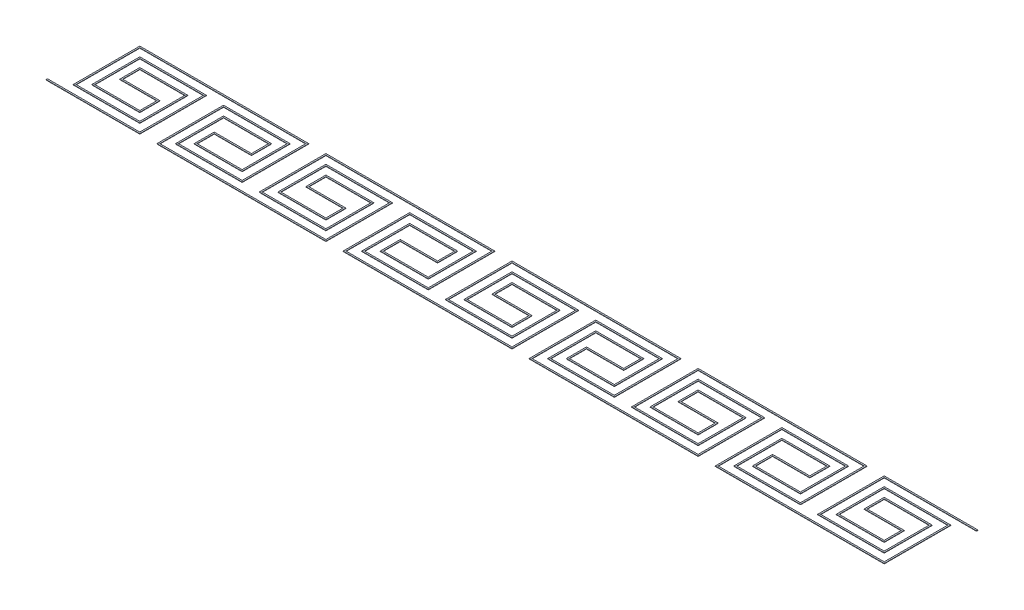
SolidWorks part; units mm, degrees
ref_plane "Front Plane" through (0, 0, 0) normal (0, 0, 1) x (1, 0, 0)
ref_plane "Top Plane" through (0, 0, 0) normal (0, 1, 0) x (1, 0, 0)
ref_plane "Right Plane" through (0, 0, 0) normal (1, 0, 0) x (0, 0, -1)
sketch "Sketch1" plane through (0, 0, 0) normal (0, 1, 0) x (1, 0, 0)
  line L0 (-0.25, 0) -> (0.25, 0)
  line L1 (-0.5, -0.5) -> (0.5, -0.5)
  line L2 (-0.5, -0.375) -> (-0.5, 0.5)
  line L3 (-0.5, 0.5) -> (0.5, 0.5)
  line L4 (0.5, -0.5) -> (0.5, 0.375)
  line L5 (-0.5, -0.5) -> (0.5, 0.5) construction
  line L6 (-0.5, 0.5) -> (0.5, -0.5) construction
  line L8 (-0.375, -0.25) -> (-0.375, 0.375)
  line L10 (0.375, -0.375) -> (0.375, 0.25)
  line L11 (-0.375, -0.375) -> (0.375, 0.375) construction
  line L12 (-0.375, 0.375) -> (0.375, -0.375) construction
  line L14 (-0.25, 0) -> (-0.25, 0.25)
  line L16 (0.25, -0.25) -> (0.25, 0)
  line L17 (-0.25, -0.25) -> (0.25, 0.25) construction
  line L18 (-0.25, 0.25) -> (0.25, -0.25) construction
  line L19 (-0.5, -0.375) -> (0.375, -0.375)
  line L20 (-0.25, 0.25) -> (0.375, 0.25)
  line L21 (-0.375, 0.375) -> (0.5, 0.375)
  line L22 (-0.5, -0.5) -> (-0.75, -0.5)
  line L23 (-0.375, -0.25) -> (0.25, -0.25)
  line L24 (-1.75, 0.5) -> (-2, 0.5)
  line L25 (-1, 0.25) -> (-1.5, -0.25) construction
  line L26 (-1, -0.25) -> (-1.5, 0.25) construction
  line L27 (-0.875, 0.375) -> (-1.625, -0.375) construction
  line L28 (-0.875, -0.375) -> (-1.625, 0.375) construction
  line L29 (-0.75, 0.5) -> (-1.75, -0.5) construction
  line L30 (-0.75, -0.5) -> (-1.75, 0.5) construction
  line L31 (-0.875, -0.25) -> (-1.5, -0.25)
  line L32 (-0.875, 0.375) -> (-1.75, 0.375)
  line L33 (-1, 0.25) -> (-1.625, 0.25)
  line L34 (-0.75, -0.375) -> (-1.625, -0.375)
  line L35 (-1.5, -0.25) -> (-1.5, 0)
  line L36 (-1, 0) -> (-1, 0.25)
  line L37 (-1.625, -0.375) -> (-1.625, 0.25)
  line L38 (-0.875, -0.25) -> (-0.875, 0.375)
  line L39 (-1.75, -0.5) -> (-1.75, 0.375)
  line L40 (-0.75, 0.5) -> (-1.75, 0.5)
  line L41 (-0.75, -0.375) -> (-0.75, 0.5)
  line L42 (-0.75, -0.5) -> (-1.75, -0.5)
  line L43 (-1, 0) -> (-1.5, 0)
  line L44 (-4.25, 0.5) -> (-4.5, 0.5)
  line L45 (-3, -0.5) -> (-2, 0.5) construction
  line L46 (-3, 0.5) -> (-2, -0.5) construction
  line L47 (-2.875, -0.375) -> (-2.125, 0.375) construction
  line L48 (-2.875, 0.375) -> (-2.125, -0.375) construction
  line L49 (-2.75, -0.25) -> (-2.25, 0.25) construction
  line L50 (-2.75, 0.25) -> (-2.25, -0.25) construction
  line L51 (-3.5, 0.25) -> (-4, -0.25) construction
  line L52 (-3.5, -0.25) -> (-4, 0.25) construction
  line L53 (-3.375, 0.375) -> (-4.125, -0.375) construction
  line L54 (-3.375, -0.375) -> (-4.125, 0.375) construction
  line L55 (-3.25, 0.5) -> (-4.25, -0.5) construction
  line L56 (-3.25, -0.5) -> (-4.25, 0.5) construction
  line L57 (-2.75, 0) -> (-2.25, 0)
  line L58 (-3, -0.5) -> (-2, -0.5)
  line L59 (-3, -0.375) -> (-3, 0.5)
  line L60 (-3, 0.5) -> (-2, 0.5)
  line L61 (-2, -0.5) -> (-2, 0.375)
  line L62 (-2.875, -0.25) -> (-2.875, 0.375)
  line L63 (-2.125, -0.375) -> (-2.125, 0.25)
  line L64 (-2.75, 0) -> (-2.75, 0.25)
  line L65 (-2.25, -0.25) -> (-2.25, 0)
  line L66 (-3, -0.375) -> (-2.125, -0.375)
  line L67 (-2.75, 0.25) -> (-2.125, 0.25)
  line L68 (-2.875, 0.375) -> (-2, 0.375)
  line L69 (-2.875, -0.25) -> (-2.25, -0.25)
  line L70 (-3.375, -0.25) -> (-4, -0.25)
  line L71 (-3.25, -0.5) -> (-3, -0.5)
  line L72 (-3.375, 0.375) -> (-4.25, 0.375)
  line L73 (-3.5, 0.25) -> (-4.125, 0.25)
  line L74 (-3.25, -0.375) -> (-4.125, -0.375)
  line L75 (-4, -0.25) -> (-4, 0)
  line L76 (-3.5, 0) -> (-3.5, 0.25)
  line L77 (-4.125, -0.375) -> (-4.125, 0.25)
  line L78 (-3.375, -0.25) -> (-3.375, 0.375)
  line L79 (-4.25, -0.5) -> (-4.25, 0.375)
  line L80 (-3.25, 0.5) -> (-4.25, 0.5)
  line L81 (-3.25, -0.375) -> (-3.25, 0.5)
  line L82 (-3.25, -0.5) -> (-4.25, -0.5)
  line L83 (-3.5, 0) -> (-4, 0)
  line L84 (-9.25, 0.5) -> (-9.5, 0.5)
  line L85 (-5.5, -0.5) -> (-4.5, 0.5) construction
  line L86 (-5.5, 0.5) -> (-4.5, -0.5) construction
  line L87 (-5.375, -0.375) -> (-4.625, 0.375) construction
  line L88 (-5.375, 0.375) -> (-4.625, -0.375) construction
  line L89 (-5.25, -0.25) -> (-4.75, 0.25) construction
  line L90 (-5.25, 0.25) -> (-4.75, -0.25) construction
  line L91 (-6, 0.25) -> (-6.5, -0.25) construction
  line L92 (-6, -0.25) -> (-6.5, 0.25) construction
  line L93 (-5.875, 0.375) -> (-6.625, -0.375) construction
  line L94 (-5.875, -0.375) -> (-6.625, 0.375) construction
  line L95 (-5.75, 0.5) -> (-6.75, -0.5) construction
  line L96 (-5.75, -0.5) -> (-6.75, 0.5) construction
  line L97 (-8, -0.5) -> (-7, 0.5) construction
  line L98 (-8, 0.5) -> (-7, -0.5) construction
  line L99 (-7.875, -0.375) -> (-7.125, 0.375) construction
  line L100 (-7.875, 0.375) -> (-7.125, -0.375) construction
  line L101 (-7.75, -0.25) -> (-7.25, 0.25) construction
  line L102 (-7.75, 0.25) -> (-7.25, -0.25) construction
  line L103 (-8.5, 0.25) -> (-9, -0.25) construction
  line L104 (-8.5, -0.25) -> (-9, 0.25) construction
  line L105 (-8.375, 0.375) -> (-9.125, -0.375) construction
  line L106 (-8.375, -0.375) -> (-9.125, 0.375) construction
  line L107 (-8.25, 0.5) -> (-9.25, -0.5) construction
  line L108 (-8.25, -0.5) -> (-9.25, 0.5) construction
  line L109 (-5.25, 0) -> (-4.75, 0)
  line L110 (-5.5, -0.5) -> (-4.5, -0.5)
  line L111 (-5.5, -0.375) -> (-5.5, 0.5)
  line L112 (-5.5, 0.5) -> (-4.5, 0.5)
  line L113 (-4.5, -0.5) -> (-4.5, 0.375)
  line L114 (-5.375, -0.25) -> (-5.375, 0.375)
  line L115 (-4.625, -0.375) -> (-4.625, 0.25)
  line L116 (-5.25, 0) -> (-5.25, 0.25)
  line L117 (-4.75, -0.25) -> (-4.75, 0)
  line L118 (-5.5, -0.375) -> (-4.625, -0.375)
  line L119 (-5.25, 0.25) -> (-4.625, 0.25)
  line L120 (-5.375, 0.375) -> (-4.5, 0.375)
  line L121 (-5.5, -0.5) -> (-5.75, -0.5)
  line L122 (-5.375, -0.25) -> (-4.75, -0.25)
  line L123 (-5.875, -0.25) -> (-6.5, -0.25)
  line L124 (-5.875, 0.375) -> (-6.75, 0.375)
  line L125 (-6, 0.25) -> (-6.625, 0.25)
  line L126 (-5.75, -0.375) -> (-6.625, -0.375)
  line L127 (-6.5, -0.25) -> (-6.5, 0)
  line L128 (-6, 0) -> (-6, 0.25)
  line L129 (-6.625, -0.375) -> (-6.625, 0.25)
  line L130 (-5.875, -0.25) -> (-5.875, 0.375)
  line L131 (-6.75, -0.5) -> (-6.75, 0.375)
  line L132 (-5.75, 0.5) -> (-6.75, 0.5)
  line L133 (-5.75, -0.375) -> (-5.75, 0.5)
  line L134 (-5.75, -0.5) -> (-6.75, -0.5)
  line L135 (-6, 0) -> (-6.5, 0)
  line L136 (-7.75, 0) -> (-7.25, 0)
  line L137 (-8, -0.5) -> (-7, -0.5)
  line L138 (-8, -0.375) -> (-8, 0.5)
  line L139 (-8, 0.5) -> (-7, 0.5)
  line L140 (-7, -0.5) -> (-7, 0.375)
  line L141 (-7.875, -0.25) -> (-7.875, 0.375)
  line L142 (-7.125, -0.375) -> (-7.125, 0.25)
  line L143 (-7.75, 0) -> (-7.75, 0.25)
  line L144 (-7.25, -0.25) -> (-7.25, 0)
  line L145 (-8, -0.375) -> (-7.125, -0.375)
  line L146 (-7.75, 0.25) -> (-7.125, 0.25)
  line L147 (-7.875, 0.375) -> (-7, 0.375)
  line L148 (-7.875, -0.25) -> (-7.25, -0.25)
  line L149 (-7, 0.5) -> (-6.75, 0.5)
  line L150 (-8.375, -0.25) -> (-9, -0.25)
  line L151 (-8.25, -0.5) -> (-8, -0.5)
  line L152 (-8.375, 0.375) -> (-9.25, 0.375)
  line L153 (-8.5, 0.25) -> (-9.125, 0.25)
  line L154 (-8.25, -0.375) -> (-9.125, -0.375)
  line L155 (-9, -0.25) -> (-9, 0)
  line L156 (-8.5, 0) -> (-8.5, 0.25)
  line L157 (-9.125, -0.375) -> (-9.125, 0.25)
  line L158 (-8.375, -0.25) -> (-8.375, 0.375)
  line L159 (-9.25, -0.5) -> (-9.25, 0.375)
  line L160 (-8.25, 0.5) -> (-9.25, 0.5)
  line L161 (-8.25, -0.375) -> (-8.25, 0.5)
  line L162 (-8.25, -0.5) -> (-9.25, -0.5)
  line L163 (-8.5, 0) -> (-9, 0)
  line L164 (0.5, 0.5) -> (0.75, 0.5)
  line L165 (-10.5, -0.5) -> (-9.5, 0.5) construction
  line L166 (-10.5, 0.5) -> (-9.5, -0.5) construction
  line L167 (-10.375, -0.375) -> (-9.625, 0.375) construction
  line L168 (-10.375, 0.375) -> (-9.625, -0.375) construction
  line L169 (-10.25, -0.25) -> (-9.75, 0.25) construction
  line L170 (-10.25, 0.25) -> (-9.75, -0.25) construction
  line L171 (-10.25, 0) -> (-9.75, 0)
  line L172 (-10.5, -0.5) -> (-9.5, -0.5)
  line L173 (-10.5, -0.375) -> (-10.5, 0.5)
  line L174 (-10.5, 0.5) -> (-9.5, 0.5)
  line L175 (-9.5, -0.5) -> (-9.5, 0.375)
  line L176 (-10.375, -0.25) -> (-10.375, 0.375)
  line L177 (-9.625, -0.375) -> (-9.625, 0.25)
  line L178 (-10.25, 0) -> (-10.25, 0.25)
  line L179 (-9.75, -0.25) -> (-9.75, 0)
  line L180 (-10.5, -0.375) -> (-9.625, -0.375)
  line L181 (-10.25, 0.25) -> (-9.625, 0.25)
  line L182 (-10.375, 0.375) -> (-9.5, 0.375)
  line L183 (-10.5, -0.5) -> (-10.75, -0.5)
  line L184 (-10.375, -0.25) -> (-9.75, -0.25)
  point P0 (0, 0)
  point P5 (0, 0)
  point P11 (0, 0)
  point P42 (-1.25, 0)
  point P79 (-2.5, 0)
  point P80 (-3.75, 0)
  point P153 (-5, 0)
  point P154 (-6.25, 0)
  point P155 (-7.5, 0)
  point P156 (-8.75, 0)
  point P176 (-10, 0)
  dimension "D1" = 1
  dimension "D2" = 0.75
  dimension "D3" = 0.5
  dimension "D4" = 0.25
sketch "Sketch2" plane through (0, 0, 0) normal (1, 0, 0) x (0, 0, -1)
  line L1 (-0.01, 0.0025) -> (0.01, 0.0025)
  line L2 (-0.01, 0.0025) -> (-0.01, -0.0025)
  line L3 (-0.01, -0.0025) -> (0.01, -0.0025)
  line L4 (0.01, 0.0025) -> (0.01, -0.0025)
  line L5 (-0.01, 0.0025) -> (0.01, -0.0025) construction
  line L6 (-0.01, -0.0025) -> (0.01, 0.0025) construction
  point P0 (0, 0)
  dimension "D1" = 0.005
  dimension "D2" = 0.02
sweep "Sweep1" add profiles "Sketch2" path "Sketch1"
